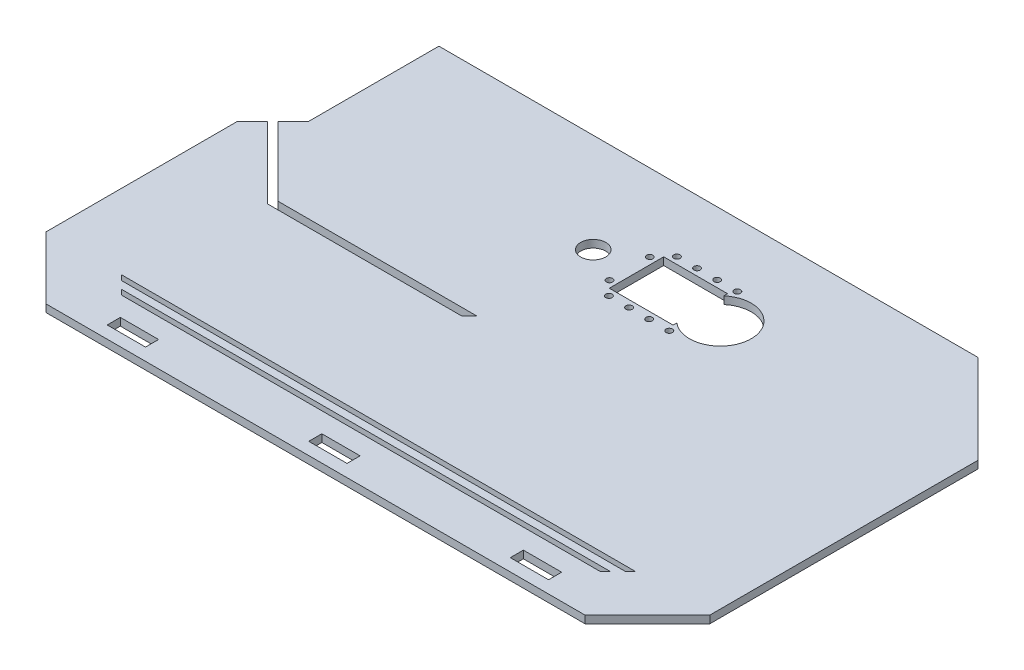
SolidWorks part; units mm, degrees
ref_plane "Front Plane" through (0, 0, 0) normal (0, 0, 1) x (1, 0, 0)
ref_plane "Top Plane" through (0, 0, 0) normal (0, 1, 0) x (1, 0, 0)
ref_plane "Right Plane" through (0, 0, 0) normal (1, 0, 0) x (0, 0, -1)
sketch "Sketch1" plane through (0, 0, 0) normal (0, 1, 0) x (1, 0, 0)
  line L0 (-107, -50) -> (-131.7487, -25.2513)
  line L1 (-107, -50) -> (107, -50)
  line L2 (96.3934, 116.5804) -> (131.7487, 81.225)
  line L3 (131.7487, -25.2513) -> (131.7487, 81.225)
  line L4 (-131.7487, 50.6173) -> (-117.6066, 64.7594)
  line L5 (0, 0) -> (0, -50) construction
  line L6 (0, 0) -> (107, 0) construction
  line L7 (-131.7487, -25.2513) -> (-131.7487, 50.6173)
  line L10 (107, -50) -> (131.7487, -25.2513)
  line L11 (-117.6066, 64.7594) -> (-117.6066, 116.5804)
  line L12 (-117.6066, 116.5804) -> (96.3934, 116.5804)
  point P0 (0, 0)
  dimension "D1" = 214
  dimension "D2" = 35
  dimension "D3" = 135
  dimension "D4" = 135
  dimension "D5" = 20
  dimension "D6" = 51.821
  dimension "D7" = 135
  dimension "D8" = 50
  dimension "D9" = 75.8685
extrude "Boss-Extrude1" add sketch "Sketch1" along normal blind 3 contours L2 L3 L10 L1 L0 L7 L4 L11 L12
sketch "Sketch2" plane through (0, 3, 0) normal (0, 1, 0) x (1, 0, 0)
  line L0 (-107, -50) -> (107, -50) construction
  line L1 (0, -50) -> (0, -60.9331) construction
  line L2 (72.5, -40) -> (87.5, -40)
  line L3 (-7.5, -40) -> (7.5, -40)
  line L4 (-7.5, -40) -> (-7.5, -45)
  line L5 (-7.5, -45) -> (7.5, -45)
  line L6 (7.5, -40) -> (7.5, -45)
  line L7 (0, -45) -> (0, -40) construction
  line L8 (-7.5, -42.5) -> (7.5, -42.5) construction
  line L9 (72.5, -40) -> (72.5, -45)
  line L10 (72.5, -45) -> (87.5, -45)
  line L11 (87.5, -40) -> (87.5, -45)
  line L12 (80, -45) -> (80, -40) construction
  line L13 (72.5, -42.5) -> (87.5, -42.5) construction
  line L14 (0, -42.5) -> (80, -42.5) construction
  line L15 (-87.5, -40) -> (-72.5, -40)
  line L16 (-87.5, -40) -> (-87.5, -45)
  line L17 (-87.5, -45) -> (-72.5, -45)
  line L18 (-72.5, -40) -> (-72.5, -45)
  line L19 (-80, -45) -> (-80, -40) construction
  line L20 (-87.5, -42.5) -> (-72.5, -42.5) construction
  line L21 (0, -42.5) -> (-80, -42.5) construction
  point P7 (0, -42.5)
  point P12 (80, -42.5)
  point P23 (-80, -42.5)
  dimension "D1" = 5
  dimension "D2" = 15
  dimension "D3" = 5
  dimension "D5" = 80
  dimension "D6" = 2
  dimension "D4" = 80
  dimension "D7" = 2
extrude "Destek Baglantı" cut sketch "Sketch2" against normal through all
sketch "Sketch5" plane through (0, 0, 0) normal (0, -1, 0) x (1, 0, 0)
  line L0 (-9.0141, -77.2399) -> (-13.4844, -77.2399) construction
  circle A0 centre (-17.0141, -77.2399) radius 5
  line B0 (23.7694, -87.7749) -> (0.4194, -87.7749) construction
  line B1 (0.4194, -87.7749) -> (0.4194, -68.1749) construction
  line B2 (0.4194, -68.1749) -> (23.7694, -68.1749) construction
  line B3 (23.7694, -68.1749) -> (23.7694, -71.1587) construction
  line B4 (23.7694, -84.791) -> (23.7694, -87.7749) construction
  line B5 (24.7694, -88.7749) -> (-0.5806, -88.7749)
  line B6 (-0.5806, -88.7749) -> (-0.5806, -67.1749)
  line B7 (-0.5806, -67.1749) -> (24.7694, -67.1749)
  line B8 (24.7694, -67.1749) -> (24.7694, -68.655)
  line B9 (24.7694, -87.2947) -> (24.7694, -88.7749)
  line B10 (-9.0141, -95.9813) -> (48.8398, -95.9813) construction
  line B11 (-9.0141, -95.9813) -> (-9.0141, -58.4985) construction
  line B12 (-9.0141, -58.4985) -> (48.8398, -58.4985) construction
  line B13 (48.8398, -95.9813) -> (48.8398, -58.4985) construction
  arc B14 (23.7694, -84.791) -> (23.7694, -71.1587) centre (32.7194, -77.9749) ccw construction
  circle B15 centre (25.9694, -91.4749) radius 1.25
  circle B16 centre (17.9694, -91.4749) radius 1.25
  circle B17 centre (9.9694, -91.4749) radius 1.25
  circle B18 centre (1.9694, -91.4749) radius 1.25
  circle B19 centre (-3.2806, -85.9749) radius 1.25
  circle B20 centre (-3.2806, -69.9749) radius 1.25
  circle B21 centre (1.9694, -64.4749) radius 1.25
  circle B22 centre (9.9694, -64.4749) radius 1.25
  circle B23 centre (17.9694, -64.4749) radius 1.25
  circle B24 centre (25.9694, -64.4749) radius 1.25
  arc B25 (24.7694, -87.2947) -> (24.7694, -68.655) centre (32.7194, -77.9749) ccw
  dimension "D1" = 10
  dimension "D2" = 8
sketch_block_instance "Block3-1"
sketch_block "Block3"
extrude "Motor" cut sketch "Sketch5" against normal through all
sketch "Sketch6" plane through (0, 3, 0) normal (0, 1, 0) x (1, 0, 0)
  line L0 (-131.7487, 50.6173) -> (-117.6066, 64.7594) construction
  line L1 (-117.6066, 64.7594) -> (-124.6777, 57.6883) construction
  line L2 (-124.6777, 57.6883) -> (-96.8327, 29.8434) construction
  line L3 (-96.8327, 29.8434) -> (-17.4541, 29.8434) construction
  line L4 (-125.7383, 56.6277) -> (-97.4541, 28.3434)
  line L5 (-97.4541, 28.3434) -> (-17.4541, 28.3434)
  line L6 (-123.617, 58.749) -> (-96.2114, 31.3434)
  line L7 (-96.2114, 31.3434) -> (-17.4541, 31.3434)
  line L8 (-125.7383, 56.6277) -> (-123.617, 58.749)
  line L9 (-17.4541, 28.3434) -> (-17.4541, 31.3434)
  dimension "D1" = 1.5
  dimension "D2" = 1.5
  dimension "D3" = 80
  dimension "D4" = 40
extrude "Cut-Extrude2" cut sketch "Sketch6" against normal through all
sketch "Sketch7" plane through (0, 3, 0) normal (0, 1, 0) x (1, 0, 0)
  line L0 (-95, -32) -> (95, -32)
  line L1 (0, -32) -> (0, -37.2993) construction
  line L2 (-107, -50) -> (107, -50) construction
  line L3 (-95, -32) -> (-97, -30)
  line L4 (0, -69.749) -> (0, -50) construction
  line L5 (-97, -30) -> (97, -30)
  line L6 (95, -32) -> (97, -30)
  line L7 (0, -25) -> (0, 10.6905) construction
  line L16 (0, 0.481) -> (0, -1.8183) construction
  line L17 (-100, -27) -> (-102, -25)
  line L18 (100, -27) -> (102, -25)
  line L19 (-100, -27) -> (100, -27)
  line L21 (-102, -25) -> (102, -25)
  dimension "D1" = 190
  dimension "D2" = 18
  dimension "D3" = 225
  dimension "D4" = 225
  dimension "D5" = 2
  dimension "D6" = 225
  dimension "D7" = 225
  dimension "D8" = 2
  dimension "D9" = 200
  dimension "D10" = 3
extrude "Cut-Extrude3" cut sketch "Sketch7" against normal through all
sketch "Sketch8" plane through (0, 3, 0) normal (0, 1, 0) x (1, 0, 0)
  line L0 (-17.4541, 31.3434) -> (-17.4541, 28.3434)
  line L1 (-17.4541, 31.3434) -> (-20.4541, 28.3434)
  line L2 (-97.4541, 28.3434) -> (-17.4541, 28.3434) construction
  line L3 (-20.4541, 28.3434) -> (-17.4541, 28.3434)
  line L4 (-17.4541, 28.3434) -> (-17.5178, 28.3472)
extrude "Boss-Extrude2" add sketch "Sketch8" against normal through all contours L0 L1 L3
sketch "Sketch9" plane through (0, 3, 0) normal (0, 1, 0) x (1, 0, 0)
  line L0 (-87.6, -39.9) -> (-72.4, -39.9)
  line L1 (-87.5, -40) -> (-72.5, -40) construction
  line L2 (-87.5, -40) -> (-87.5, -45) construction
  line L3 (-87.5, -45) -> (-72.5, -45) construction
  line L4 (-72.5, -40) -> (-72.5, -45) construction
  line L5 (-72.4, -39.9) -> (-72.4, -45.1)
  line L6 (-87.6, -45.1) -> (-72.4, -45.1)
  line L7 (-87.6, -39.9) -> (-87.6, -45.1)
  line L8 (-7.6, -39.9) -> (7.6, -39.9)
  line L9 (7.6, -39.9) -> (7.6, -45.1)
  line L10 (-7.6, -45.1) -> (7.6, -45.1)
  line L11 (-7.6, -39.9) -> (-7.6, -45.1)
  line L12 (-7.5, -40) -> (7.5, -40) construction
  line L13 (-7.5, -40) -> (-7.5, -45) construction
  line L14 (-7.5, -45) -> (7.5, -45) construction
  line L15 (7.5, -40) -> (7.5, -45) construction
  line L16 (72.4, -39.9) -> (87.6, -39.9)
  line L17 (87.6, -39.9) -> (87.6, -45.1)
  line L18 (72.4, -45.1) -> (87.6, -45.1)
  line L19 (72.4, -39.9) -> (72.4, -45.1)
  line L20 (72.5, -40) -> (87.5, -40) construction
  line L21 (72.5, -40) -> (72.5, -45) construction
  line L22 (72.5, -45) -> (87.5, -45) construction
  line L23 (87.5, -40) -> (87.5, -45) construction
  dimension "D1" = 0.1
  dimension "D2" = 3
extrude "Destek Baglanti Ofset" cut sketch "Sketch9" against normal through all
